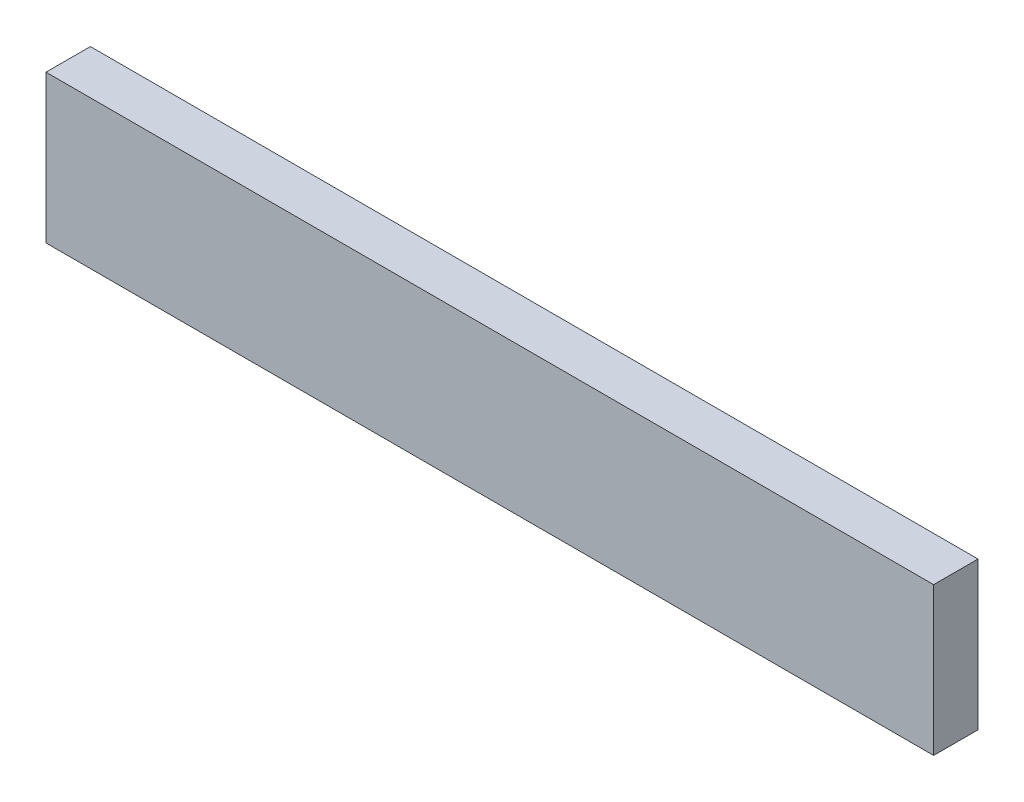
SolidWorks part; units mm, degrees
ref_plane "Alzado" through (0, 0, 0) normal (0, 0, 1) x (1, 0, 0)
ref_plane "Planta" through (0, 0, 0) normal (0, 1, 0) x (1, 0, 0)
ref_plane "Vista lateral" through (0, 0, 0) normal (1, 0, 0) x (0, 0, -1)
sketch "Croquis1" plane through (0, 0, 0) normal (0, 0, 1) x (1, 0, 0)
  line L0 (-78.2361, 45.4028) -> (74.1639, 45.4028)
  line L1 (74.1639, 45.4028) -> (74.1639, 20.0028)
  line L2 (74.1639, 20.0028) -> (-78.2361, 20.0028)
  line L3 (-78.2361, 45.4028) -> (-78.2361, 20.0028)
extrude "Saliente-Extruir1" add sketch "Croquis1" along normal blind 7.62
